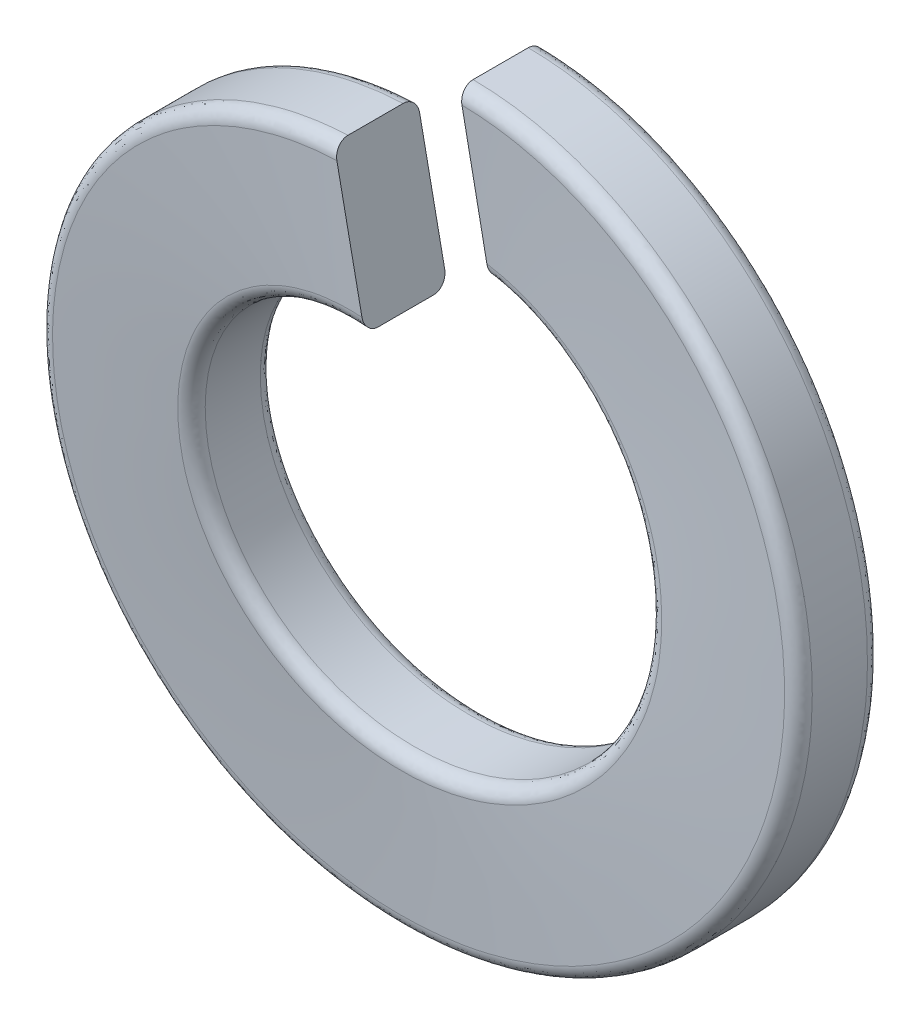
SolidWorks part; units mm, degrees
material "Plain Carbon Steel"
ref_plane "Front Plane" through (0, 0, 0) normal (0, 0, 1) x (1, 0, 0)
ref_plane "Top Plane" through (0, 0, 0) normal (0, 1, 0) x (1, 0, 0)
ref_plane "Right Plane" through (0, 0, 0) normal (1, 0, 0) x (0, 0, -1)
sketch "Sketch1" plane through (0, 0, 0) normal (0, 0, 1) x (1, 0, 0)
  line L0 (0, -2.55) -> (0, 2.55) construction
  line L1 (-0.1112, 2.5476) -> (0.1134, 1.4456) construction
  line L2 (0, 0) -> (-0.725, -1.2557) construction
  line L3 (0, 1.45) -> (-0.2222, 2.5403) construction
  line L4 (0, 0) -> (-0.2222, 2.5403) construction
  line L5 (-0.1112, 2.5476) -> (0, 0) construction
  circle A0 centre (0, 0) radius 2.55 construction
  circle A1 centre (0, 0) radius 1.45 construction
  point P6 (0, -1.45)
  dimension "ID" = 2.9
  dimension "OD" = 5.1
  dimension "D2" = 5
  dimension "D1" = 30
  dimension "D3" = 2.5
sketch "Sketch2" plane through (0, 0, 0) normal (1, 0, 0) x (0, 0, -1)
  line L0 (-0.7, 0) -> (0.7, 0) construction
  line L1 (0, -2.55) -> (0, 2.55) construction
  line L2 (-0.7, 2.55) -> (-0.1, 2.55) construction
  line L3 (-0.7, 2.55) -> (-0.7, 1.45) construction
  line L4 (-0.7, 1.45) -> (-0.1, 1.45) construction
  line L5 (-0.1, 2.55) -> (-0.1, 1.45) construction
  line L6 (0, -2.55) -> (0, 2.55) construction
  line L12 (-0.3, -1.45) -> (0.3, -1.45) construction
  line L13 (-0.3, -1.45) -> (-0.3, -2.55) construction
  line L14 (-0.3, -2.55) -> (0.3, -2.55) construction
  line L15 (0.3, -1.45) -> (0.3, -2.55) construction
  point P8 (-0.4, 2.55)
  point P13 (0.3, -2.45)
  point P15 (0.7, 2.55)
  point P19 (0.4, 2.55)
  dimension "Thickness" = 0.6
  dimension "Helix Height" = 0.8
  dimension "Height" = 1.4
  dimension "Radius" = 0.1
ref_plane "Plane1" through (0, 0, 0.4) normal (0, 0, 1) x (1, 0, 0)
sketch "Sketch3" plane through (0, 0, 0.4) normal (0, 0, 1) x (1, 0, 0)
  circle A0 centre (0, 0) radius 2.55 construction
  circle A1 centre (0, 0) radius 2.55
curve "Helix/Spiral1" pitch 0.8008 height 0.8 turns 0.999
ref_plane "Plane2" through (0.2838, 0.0578, 0) normal (0.9799, 0.1997, 0) x (0.007, -0.0343, -0.9994)
sketch "Sketch4" plane through (0.3127, -0.084, 0.0051) normal (0.9799, 0.1997, 0) x (0.007, -0.0343, -0.9994)
  line L0 (-0.787, 2.6174) -> (-0.1873, 2.6384) construction
  line L10 (-0.7493, 1.5402) -> (-0.1496, 1.5612) construction
  line L12 (-0.7882, 2.6523) -> (-0.1885, 2.6733)
  line L13 (-0.1885, 2.6733) -> (-0.1496, 1.5612)
  line L14 (-0.7493, 1.5402) -> (-0.1496, 1.5612)
  line L15 (-0.7882, 2.6523) -> (-0.7493, 1.5402)
sweep "Sweep1" add profiles "Sketch4" path "Helix/Spiral1"
sketch "Sketch5" plane through (0, 0, 0) normal (0, 0, 1) x (1, 0, 0)
  line L0 (0, 1.45) -> (-0.2222, 2.5403) construction
  line L1 (-0.1112, 2.5476) -> (0.1134, 1.4456) construction
  line L2 (0, 1.45) -> (-0.2222, 2.5403)
  line L3 (-0.1112, 2.5476) -> (0.1134, 1.4456)
  circle A0 centre (0, 0) radius 1.45 construction
  circle A1 centre (0, 0) radius 2.55 construction
  arc A2 (0.1134, 1.4456) -> (0, 1.45) centre (0, 0) ccw
  arc A3 (-0.1112, 2.5476) -> (-0.2222, 2.5403) centre (0, 0) ccw
extrude "Cut-Extrude1" cut sketch "Sketch5" against normal through all
fillet "Fillet1" radius 0.1 4 edges
equation "\"D3@Helix/Spiral1\"=\"Helix Height@Sketch2\""
equation "\"D7@Helix/Spiral1\"=90+\"D2@Sketch1\""
equation "\"D1@Fillet1\"=\"Radius@Sketch2\""
equation "\"D3@Sketch1\"=\"D2@Sketch1\"/2"
